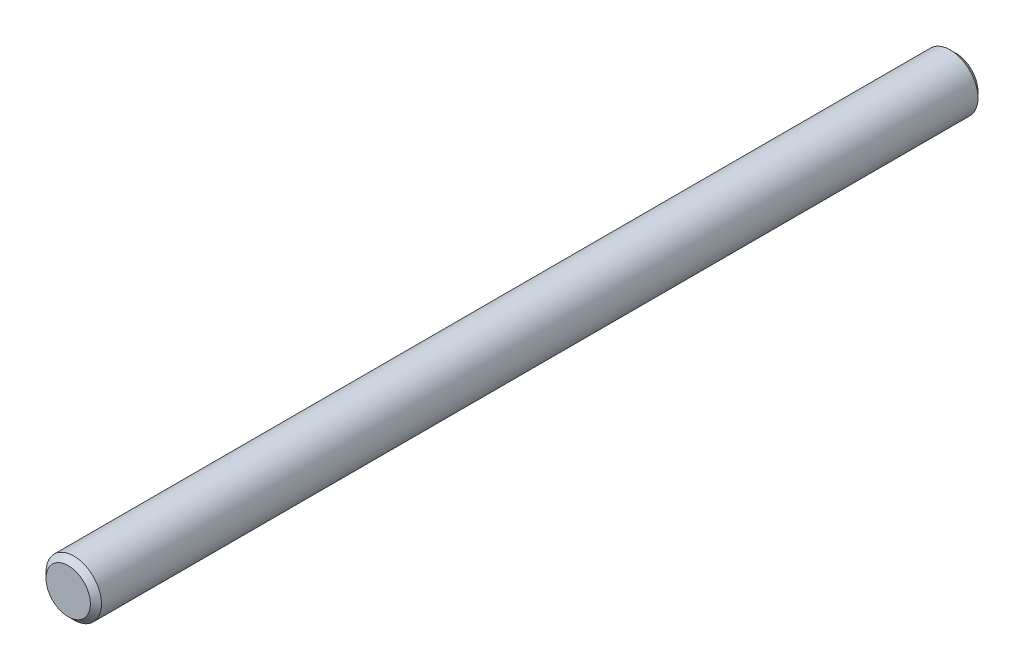
SolidWorks part; units mm, degrees
material "Plain Carbon Steel"
ref_plane "Front" through (0, 0, 0) normal (0, 0, 1) x (1, 0, 0)
ref_plane "Top" through (0, 0, 0) normal (0, 1, 0) x (1, 0, 0)
ref_plane "Right" through (0, 0, 0) normal (1, 0, 0) x (0, 0, -1)
sketch "Sketch1" plane through (0, 0, 0) normal (0, 0, 1) x (1, 0, 0)
  circle A0 centre (0, 0) radius 9.525
  dimension "dia" = 19.05
extrude "Extrude1" add sketch "Sketch1" along normal mid plane 304.8
sketch "Sketch2" plane through (0, 0, 0) normal (1, 0, 0) x (0, 0, -1)
  line L0 (152.4, 9.525) -> (149.86, 9.525) construction
  line L1 (152.4, 9.525) -> (-152.4, 9.525) construction
  line L2 (149.86, 9.525) -> (118.9037, 9.525) construction
  line L3 (118.9037, 9.525) -> (111.76, 9.525) construction
  line L4 (111.76, 9.525) -> (109.22, 9.525) construction
  line L5 (109.22, 9.525) -> (107.7011, 9.525) construction
  line L7 (101.3511, 9.525) -> (96.4159, 9.525) construction
  line L8 (96.4159, 9.525) -> (86.4006, 9.525) construction
  line L10 (-152.4, -9.525) -> (152.4, -9.525) construction
  line L11 (-152.4, 9.525) -> (-149.86, 9.525) construction
  line L12 (-149.86, 9.525) -> (-149.86, -9.525) construction
  line L13 (107.7011, 9.525) -> (101.3511, 9.525) construction
  line L14 (101.3511, 9.525) -> (101.3511, -9.525) construction
  line L15 (111.76, 9.525) -> (111.76, -9.525) construction
  line L16 (86.4006, 9.525) -> (81.4654, 9.525) construction
  line L17 (81.4654, 9.525) -> (71.4578, 9.525) construction
  line L18 (71.4578, 9.525) -> (66.5226, 9.525) construction
  line L19 (66.5226, 9.525) -> (56.515, 9.525) construction
  line L20 (86.4006, 9.525) -> (86.4006, -9.525) construction
  line L21 (71.4578, 9.525) -> (71.4578, -9.525) construction
  line L22 (56.515, 9.525) -> (56.515, -9.525) construction
  line L23 (56.515, 9.525) -> (51.5874, 9.525) construction
  line L24 (51.5874, 9.525) -> (41.5798, 9.525) construction
  line L25 (41.5798, 9.525) -> (41.5798, -9.525) construction
  line L26 (41.5798, 9.525) -> (36.6522, 9.525) construction
  line L27 (36.6522, 9.525) -> (26.6446, 9.525) construction
  line L28 (26.6446, 9.525) -> (21.717, 9.525) construction
  line L29 (21.717, 9.525) -> (11.7094, 9.525) construction
  line L30 (26.6446, 9.525) -> (26.6446, -9.525) construction
  line L31 (11.7094, 9.525) -> (11.7094, -9.525) construction
  line L32 (11.7094, 9.525) -> (6.7742, 9.525) construction
  line L33 (6.7742, 9.525) -> (0.4242, 9.525) construction
  line L34 (0.4242, 9.525) -> (-1.0947, 9.525) construction
  line L35 (-1.0947, 9.525) -> (-3.6347, 9.525) construction
  line L36 (-3.6347, 9.525) -> (-3.6347, -9.525) construction
  line L37 (-3.6347, 9.525) -> (-54.4347, 9.525) construction
  line L38 (-54.4347, 9.525) -> (-54.4347, -9.525) construction
  point P0 (-152.4, 9.525)
  point P1 (152.4, 9.525)
  dimension "D1" = 2.54
  dimension "D2" = 30.9562
  dimension "D3" = 7.1437
  dimension "D4" = 2.54
  dimension "D5" = 1.5189
  dimension "D6" = 6.35
  dimension "D7" = 10.0152
  dimension "D8" = 2.54
  dimension "D9" = 4.9352
  dimension "D10" = 4.9352
  dimension "D11" = 10.0076
  dimension "D12" = 4.9352
  dimension "D13" = 10.0076
  dimension "D14" = 4.9276
  dimension "D15" = 10.0076
  dimension "D16" = 4.9276
  dimension "D17" = 10.0076
  dimension "D18" = 4.9276
  dimension "D19" = 10.0076
  dimension "D20" = 4.9352
  dimension "D21" = 6.35
  dimension "D22" = 1.5189
  dimension "D23" = 2.54
  dimension "D24" = 50.8
chamfer "Chamfer1" distance 1.905 angle 45 2 edges at (9.525, 0, -152.4) (9.525, 0, 152.4)
equation "\"D1@Chamfer1\" = \"dia@Sketch1\" * .1"
